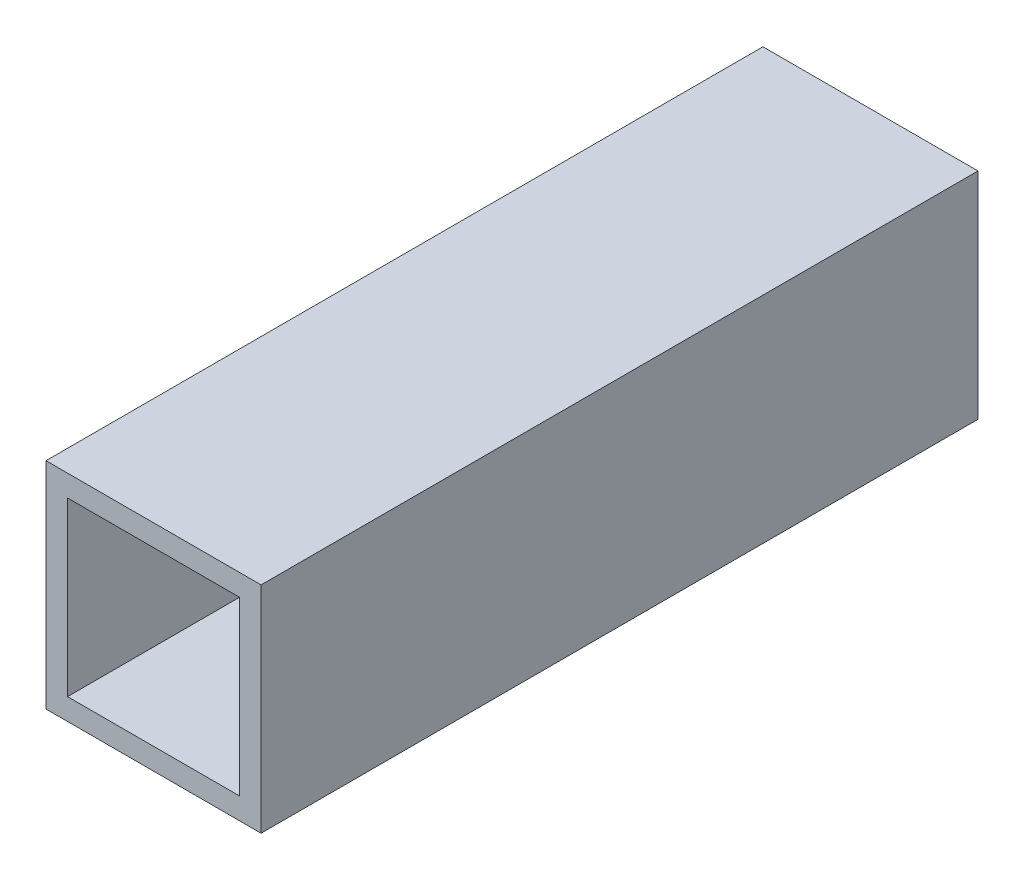
SolidWorks part; units mm, degrees
material "1060 合金"
ref_plane "正面" through (0, 0, 0) normal (0, 0, 1) x (1, 0, 0)
ref_plane "平面" through (0, 0, 0) normal (0, 1, 0) x (1, 0, 0)
ref_plane "右側面" through (0, 0, 0) normal (1, 0, 0) x (0, 0, -1)
sketch "ｽｹｯﾁ1" plane through (0, 0, 0) normal (0, 0, 1) x (1, 0, 0)
  line L1 (-7.0101, 7.7326) -> (7.9899, 7.7326)
  line L2 (-7.0101, 7.7326) -> (-7.0101, -7.2674)
  line L3 (-7.0101, -7.2674) -> (7.9899, -7.2674)
  line L4 (7.9899, 7.7326) -> (7.9899, -7.2674)
  line L9 (-5.5101, 6.2326) -> (6.4899, 6.2326)
  line L10 (-5.5101, 6.2326) -> (-5.5101, -5.7674)
  line L11 (-5.5101, -5.7674) -> (6.4899, -5.7674)
  line L12 (6.4899, 6.2326) -> (6.4899, -5.7674)
  dimension "D1" = 15
  dimension "D2" = 15
  dimension "D3" = 1.5
  dimension "D4" = 1.5
  dimension "D5" = 12
  dimension "D6" = 12
extrude "ﾎﾞｽ - 押し出し2" add sketch "ｽｹｯﾁ1" along normal blind 50
